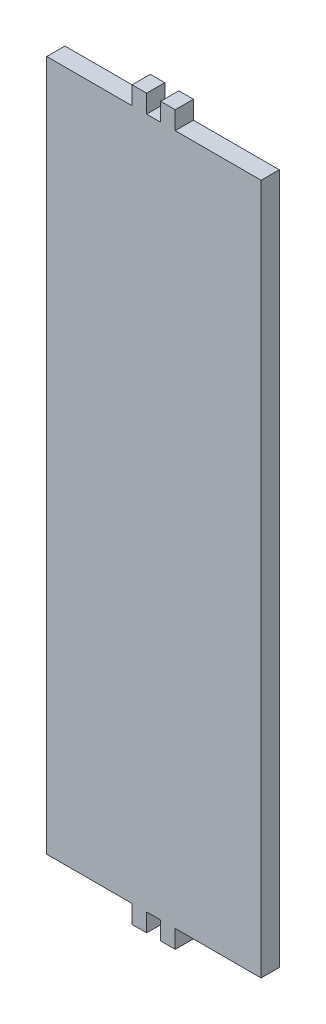
SolidWorks part; units mm, degrees
ref_plane "Front Plane" through (0, 0, 0) normal (0, 0, 1) x (1, 0, 0)
ref_plane "Top Plane" through (0, 0, 0) normal (0, 1, 0) x (1, 0, 0)
ref_plane "Right Plane" through (0, 0, 0) normal (1, 0, 0) x (0, 0, -1)
sketch "Sketch1" plane through (0, 0, 0) normal (0, 0, 1) x (1, 0, 0)
  line L0 (24.9057, 0) -> (-24.9057, 0) construction
  line L1 (-24.9057, -120.6625) -> (24.9057, -120.6625)
  line L2 (-24.9057, -120.6625) -> (-24.9057, 120.6625)
  line L3 (-24.9057, 120.6625) -> (24.9057, 120.6625)
  line L4 (24.9057, -120.6625) -> (24.9057, 120.6625)
  line L5 (-24.9057, -120.6625) -> (24.9057, 120.6625) construction
  line L6 (-24.9057, 120.6625) -> (24.9057, -120.6625) construction
  line L7 (19.9057, -120.6625) -> (19.9057, -127.0125)
  line L8 (4.9057, 120.6625) -> (9.9057, 120.6625)
  line L9 (4.9057, 120.6625) -> (4.9057, 127.0125)
  line L10 (4.9057, 127.0125) -> (9.9057, 127.0125)
  line L11 (9.9057, 120.6625) -> (9.9057, 127.0125)
  line L12 (14.9057, 120.6625) -> (19.9057, 120.6625)
  line L13 (14.9057, 120.6625) -> (14.9057, 127.0125)
  line L14 (14.9057, 127.0125) -> (19.9057, 127.0125)
  line L15 (19.9057, 120.6625) -> (19.9057, 127.0125)
  line L16 (14.9057, -127.0125) -> (19.9057, -127.0125)
  line L17 (14.9057, -120.6625) -> (14.9057, -127.0125)
  line L18 (9.9057, -120.6625) -> (9.9057, -127.0125)
  line L19 (4.9057, -127.0125) -> (9.9057, -127.0125)
  line L20 (4.9057, -120.6625) -> (4.9057, -127.0125)
  line L22 (24.9057, 120.6625) -> (49.9057, 120.6625)
  line L23 (24.9057, 120.6625) -> (24.9057, -120.6625)
  line L24 (24.9057, -120.6625) -> (49.9057, -120.6625)
  line L25 (49.9057, 120.6625) -> (49.9057, -120.6625)
  point P0 (0, 0)
  dimension "D1" = 241.325
  dimension "D2" = 49.8113
  dimension "D3" = 5
  dimension "D4" = 5
  dimension "D5" = 5
  dimension "D6" = 6.35
  dimension "D7" = 25
extrude "Boss-Extrude1" add sketch "Sketch1" along normal blind 6.35 contours L1 L4 L3 L2 | L3 L15 L14 L13 | L3 L11 L10 L9 | L1 L20 L19 L18 | L1 L17 L16 L7 | L25 L22 L4 L24
sketch "Sketch2" plane through (0, 0, 6.35) normal (0, 0, 1) x (1, 0, 0)
  line L20 (49.9463, -120.7031) -> (49.9463, 120.7031)
  line L21 (49.9463, -120.7031) -> (49.9463, 120.7031)
  line L40 (-24.9463, -120.7031) -> (4.865, -120.7031)
  line L41 (4.865, -120.7031) -> (4.865, -127.0531)
  line L42 (4.865, -127.0531) -> (9.9463, -127.0531)
  line L43 (9.9463, -127.0531) -> (9.9463, -120.7031)
  line L44 (9.9463, -120.7031) -> (14.865, -120.7031)
  line L45 (14.865, -120.7031) -> (14.865, -127.0531)
  line L46 (14.865, -127.0531) -> (19.9463, -127.0531)
  line L47 (19.9463, -127.0531) -> (19.9463, -120.7031)
  line L48 (19.9463, -120.7031) -> (49.9463, -120.7031)
  line L50 (49.9463, 120.7031) -> (19.9463, 120.7031)
  line L51 (19.9463, 120.7031) -> (19.9463, 127.0531)
  line L52 (19.9463, 127.0531) -> (14.865, 127.0531)
  line L53 (14.865, 127.0531) -> (14.865, 120.7031)
  line L54 (14.865, 120.7031) -> (9.9463, 120.7031)
  line L55 (9.9463, 120.7031) -> (9.9463, 127.0531)
  line L56 (9.9463, 127.0531) -> (4.865, 127.0531)
  line L57 (4.865, 127.0531) -> (4.865, 120.7031)
  line L58 (4.865, 120.7031) -> (-24.9463, 120.7031)
  line L59 (-24.9463, 120.7031) -> (-24.9463, -120.7031)
  line L60 (-24.9463, -120.7031) -> (4.865, -120.7031)
  line L61 (4.865, -120.7031) -> (4.865, -127.0531)
  line L62 (4.865, -127.0531) -> (9.9463, -127.0531)
  line L63 (9.9463, -127.0531) -> (9.9463, -120.7031)
  line L64 (9.9463, -120.7031) -> (14.865, -120.7031)
  line L65 (14.865, -120.7031) -> (14.865, -127.0531)
  line L66 (14.865, -127.0531) -> (19.9463, -127.0531)
  line L67 (19.9463, -127.0531) -> (19.9463, -120.7031)
  line L68 (19.9463, -120.7031) -> (49.9463, -120.7031)
  line L70 (49.9463, 120.7031) -> (19.9463, 120.7031)
  line L71 (19.9463, 120.7031) -> (19.9463, 127.0531)
  line L72 (19.9463, 127.0531) -> (14.865, 127.0531)
  line L73 (14.865, 127.0531) -> (14.865, 120.7031)
  line L74 (14.865, 120.7031) -> (9.9463, 120.7031)
  line L75 (9.9463, 120.7031) -> (9.9463, 127.0531)
  line L76 (9.9463, 127.0531) -> (4.865, 127.0531)
  line L77 (4.865, 127.0531) -> (4.865, 120.7031)
  line L78 (4.865, 120.7031) -> (-24.9463, 120.7031)
  line L79 (-24.9463, 120.7031) -> (-24.9463, -120.7031)
  dimension "D1" = 0.0406
extrude "Boss-Extrude2" add sketch "Sketch2" against normal up to surface (6.35 mm away) up to face at (12.4245, 0, 0)
